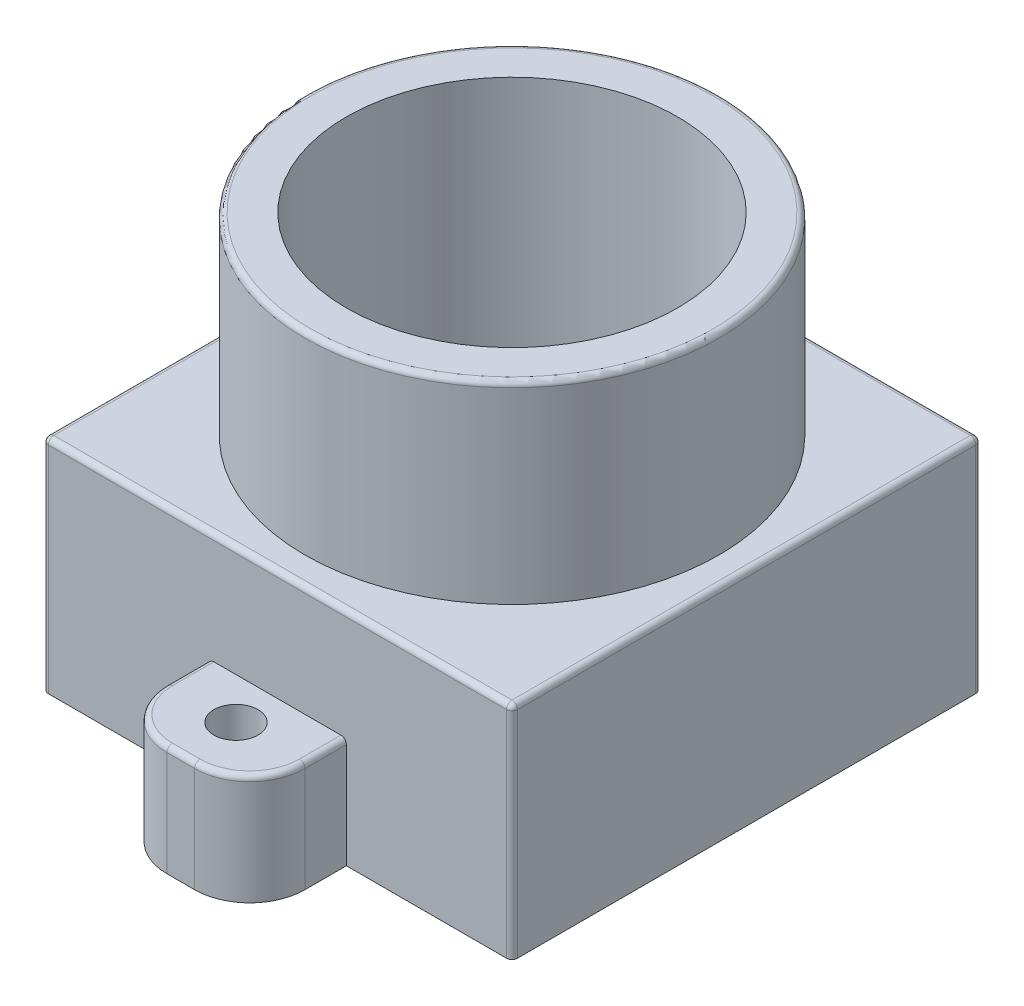
SolidWorks part; units mm, degrees
material "ﾀﾞｸﾀｲﾙ鋳鉄"
ref_plane "正面" through (0, 0, 0) normal (0, 0, 1) x (1, 0, 0)
ref_plane "平面" through (0, 0, 0) normal (0, 1, 0) x (1, 0, 0)
ref_plane "右側面" through (0, 0, 0) normal (1, 0, 0) x (0, 0, -1)
sketch "Sketch1" plane through (0, 0, 0) normal (0, 1, 0) x (1, 0, 0)
  line L1 (-8.5, 8.5) -> (8.5, 8.5)
  line L2 (-8.5, 8.5) -> (-8.5, -8.5)
  line L3 (-8.5, -8.5) -> (8.5, -8.5)
  line L4 (8.5, 8.5) -> (8.5, -8.5)
  line L5 (-8.5, 8.5) -> (8.5, -8.5) construction
  line L6 (-8.5, -8.5) -> (8.5, 8.5) construction
  point P0 (0, 0)
  dimension "D1" = 17
  dimension "D2" = 17
extrude "Boss-Extrude1" add sketch "Sketch1" along normal blind 8
sketch "Sketch2" plane through (0, 0, 8.5) normal (0, 0, 1) x (1, 0, 0)
  line L0 (-8.5, 0) -> (8.5, 0) construction
  line L1 (-2.5, 0) -> (2.5, 0)
  line L2 (-2.5, 0) -> (-2.5, 4)
  line L3 (-2.5, 4) -> (2.5, 4)
  line L4 (2.5, 0) -> (2.5, 4)
  line L5 (-8.5, 8) -> (-8.5, 0) construction
  line L6 (8.5, 8) -> (8.5, 0) construction
  dimension "D1" = 6
  dimension "D2" = 6
  dimension "D3" = 4
extrude "Boss-Extrude2" add sketch "Sketch2" along normal blind 3.5
sketch "Sketch3" plane through (0, 0, -8.5) normal (0, 0, -1) x (-1, 0, 0)
  line L0 (-8.5, 0) -> (8.5, 0) construction
  line L1 (-2.5, 0) -> (2.5, 0)
  line L2 (-2.5, 0) -> (-2.5, 4)
  line L3 (-2.5, 4) -> (2.5, 4)
  line L4 (2.5, 0) -> (2.5, 4)
  line L5 (-8.5, 8) -> (-8.5, 0) construction
  line L6 (8.5, 8) -> (8.5, 0) construction
  dimension "D1" = 6
  dimension "D2" = 6
  dimension "D3" = 4
extrude "Boss-Extrude3" add sketch "Sketch3" along normal blind 3.5
sketch "Sketch4" plane through (0, 4, 0) normal (0, 1, 0) x (1, 0, 0)
  line L1 (-2.5, 8.5) -> (-1, 8.5)
  line L2 (-2.5, 8.5) -> (-2.5, 10)
  line L3 (-2.5, 10) -> (-1, 10)
  line L4 (-1, 8.5) -> (-1, 10)
  line L5 (-2.5, -8.5) -> (-1, -8.5)
  line L6 (-2.5, -8.5) -> (-2.5, -10)
  line L7 (-2.5, -10) -> (-1, -10)
  line L8 (-1, -8.5) -> (-1, -10)
hole_wizard "M2x0.4 Tapped Hole1" positions "Sketch6" profile "Sketch7" tap size "M2x0.4" standard "JIS" end condition through all
sketch "Sketch6" plane through (0, 4, 0) normal (0, 1, 0) x (1, 0, 0)
  line L0 (2.5, 12) -> (2.5, 8.5) construction
  line L1 (2.5, -12) -> (2.5, -8.5) construction
  point P6 (0, -10)
  point P8 (0, 10)
  point P11 (0, 0)
  point P12 (0, 0)
  dimension "D1" = 2.5
  dimension "D2" = 2.5
sketch "Sketch7" plane through (0, 4, 10) normal (1, 0, 0) x (0, 0, 1)
  line L0 (0, 0) -> (0, 4)
  line L1 (0, 4) -> (0.8, 4)
  line L2 (0.8, 4) -> (0.8, 0)
  line L5 (0.8, 0) -> (0, 0)
  line L11 (0, -6.35) -> (0, 107.95) construction
  dimension "Thru Tap Drill Dia." = 1.6
  dimension "Thru Tap Drill Depth" = 4
cosmetic thread "Hole Thread1" parameters "D2"=2
cosmetic thread "Hole Thread2" parameters "D2"=2
fillet "Fillet1" radius 2 4 edges at (-2.5, 2, 12) (2.5, 2, 12) (-2.5, 2, -12) (2.5, 2, -12)
sketch "Sketch8" plane through (0, 8, 0) normal (0, 1, 0) x (1, 0, 0)
  circle A0 centre (0, 0) radius 7.5
extrude "Boss-Extrude4" add sketch "Sketch8" along normal blind 7
sketch "Sketch9" plane through (0, 15, 0) normal (0, 1, 0) x (1, 0, 0)
  circle A0 centre (0, 0) radius 6
extrude "Cut-Extrude1" cut sketch "Sketch9" against normal through all
fillet "Fillet2" radius 0.2 19 edges at (0, 15, 7.5) (8.5, 4, 8.5) (8.5, 4, -8.5) (-8.5, 4, 8.5) (-8.5, 4, -8.5) (2.5, 4, 9.25) (1.9142, 4, 11.4142) (-1.9142, 4, 11.4142) (-2.5, 4, 9.25) (0, 8, 8.5) (8.5, 8, 0) (-8.5, 8, 0) (0, 8, -8.5) (2.5, 4, -9.25) (1.9142, 4, -11.4142) (-1.9142, 4, -11.4142) (-2.5, 4, -9.25) (0, 4, 12) (0, 4, -12)
